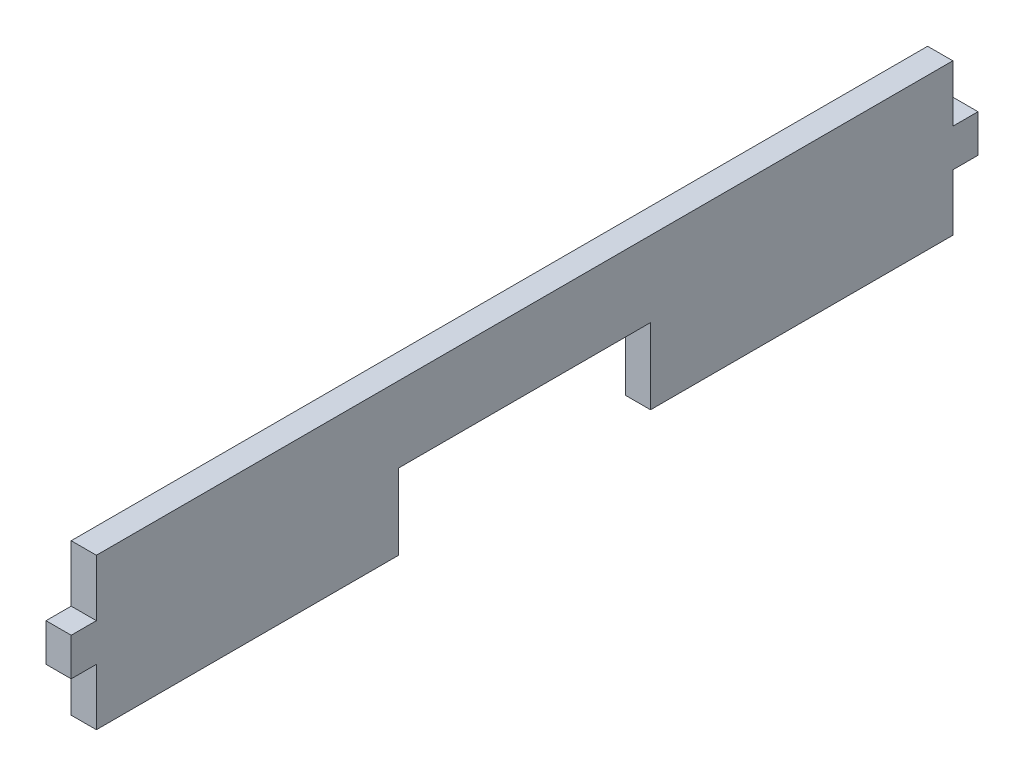
SolidWorks part; units mm, degrees
ref_plane "Front Plane" through (0, 0, 0) normal (0, 0, 1) x (1, 0, 0)
ref_plane "Top Plane" through (0, 0, 0) normal (0, 1, 0) x (1, 0, 0)
ref_plane "Right Plane" through (0, 0, 0) normal (1, 0, 0) x (0, 0, -1)
sketch "Sketch1" plane through (0, 0, 0) normal (1, 0, 0) x (0, 0, -1)
  line L0 (-43.18, 7.62) -> (-43.18, 1.905)
  line L1 (-43.18, 7.62) -> (43.18, 7.62)
  line L2 (-43.18, 7.62) -> (-43.18, -7.62) construction
  line L3 (-43.18, -7.62) -> (43.18, -7.62)
  line L4 (43.18, 7.62) -> (43.18, -7.62) construction
  line L5 (-43.18, 7.62) -> (43.18, -7.62) construction
  line L6 (-43.18, -7.62) -> (43.18, 7.62) construction
  line L7 (-43.18, 1.905) -> (-45.72, 1.905)
  line L8 (-45.72, 1.905) -> (-45.72, -1.905)
  line L9 (-45.72, -1.905) -> (-43.18, -1.905)
  line L10 (-43.18, -1.905) -> (-43.18, -7.62)
  line L11 (-43.18, 0) -> (43.18, 0) construction
  line L12 (0, 7.62) -> (0, -7.62) construction
  line L13 (43.18, -1.905) -> (43.18, -7.62)
  line L14 (45.72, -1.905) -> (43.18, -1.905)
  line L15 (45.72, 1.905) -> (45.72, -1.905)
  line L16 (43.18, 1.905) -> (45.72, 1.905)
  line L17 (43.18, 7.62) -> (43.18, 1.905)
  point P0 (0, 0)
  dimension "D1" = 86.36
  dimension "D2" = 15.24
  dimension "D3" = 3.81
  dimension "D4" = 2.54
extrude "Boss-Extrude1" add sketch "Sketch1" along normal blind 2.54
sketch "Sketch2" plane through (2.54, 0, 0) normal (1, 0, 0) x (0, 0, -1)
  line L0 (-43.18, -7.62) -> (43.18, -7.62) construction
  line L1 (-12.7, 0) -> (12.7, 0)
  line L2 (-12.7, 0) -> (-12.7, -7.62)
  line L3 (-12.7, -7.62) -> (12.7, -7.62)
  line L4 (12.7, 0) -> (12.7, -7.62)
  line L5 (-12.7, 0) -> (12.7, -7.62) construction
  line L6 (-12.7, -7.62) -> (12.7, 0) construction
  point P0 (0, -3.81)
  dimension "D1" = 25.4
extrude "Cut-Extrude1" cut sketch "Sketch2" against normal up to next
